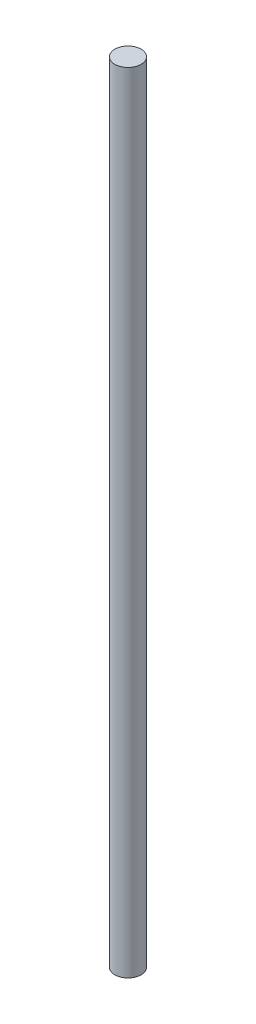
SolidWorks part; units mm, degrees
material "3003 Alloy"
ref_plane "Front Plane" through (0, 0, 0) normal (0, 0, 1) x (1, 0, 0)
ref_plane "Top Plane" through (0, 0, 0) normal (0, 1, 0) x (1, 0, 0)
ref_plane "Right Plane" through (0, 0, 0) normal (1, 0, 0) x (0, 0, -1)
sketch "Sketch1" plane through (0, 0, 0) normal (0, 1, 0) x (1, 0, 0)
  circle A0 centre (0, 0) radius 0.25
  dimension "D1" = 0.5
extrude "Boss-Extrude1" add sketch "Sketch1" along normal mid plane 15
